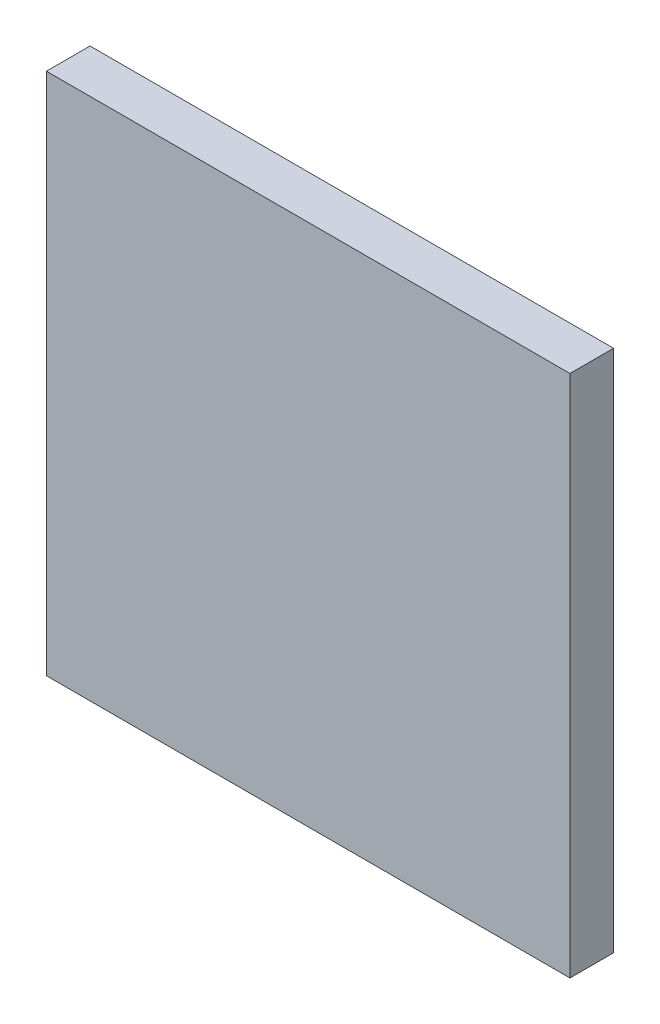
SolidWorks part; units mm, degrees
material "Acrylic (Medium-high impact)"
ref_plane "Front" through (0, 0, 0) normal (0, 0, 1) x (1, 0, 0)
ref_plane "Top" through (0, 0, 0) normal (0, 1, 0) x (1, 0, 0)
ref_plane "Right" through (0, 0, 0) normal (1, 0, 0) x (0, 0, -1)
sketch "Sketch1" plane through (0, 0, 0) normal (0, 0, 1) x (1, 0, 0)
  line L1 (-38.1, 38.1) -> (38.1, 38.1)
  line L2 (-38.1, 38.1) -> (-38.1, -38.1)
  line L3 (-38.1, -38.1) -> (38.1, -38.1)
  line L4 (38.1, 38.1) -> (38.1, -38.1)
  point P4 (0, 38.1)
  point P6 (38.1, 0)
  dimension "D1" = 76.2
  dimension "D2" = 76.2
extrude "Boss-Extrude1" add sketch "Sketch1" along normal blind 6.35
